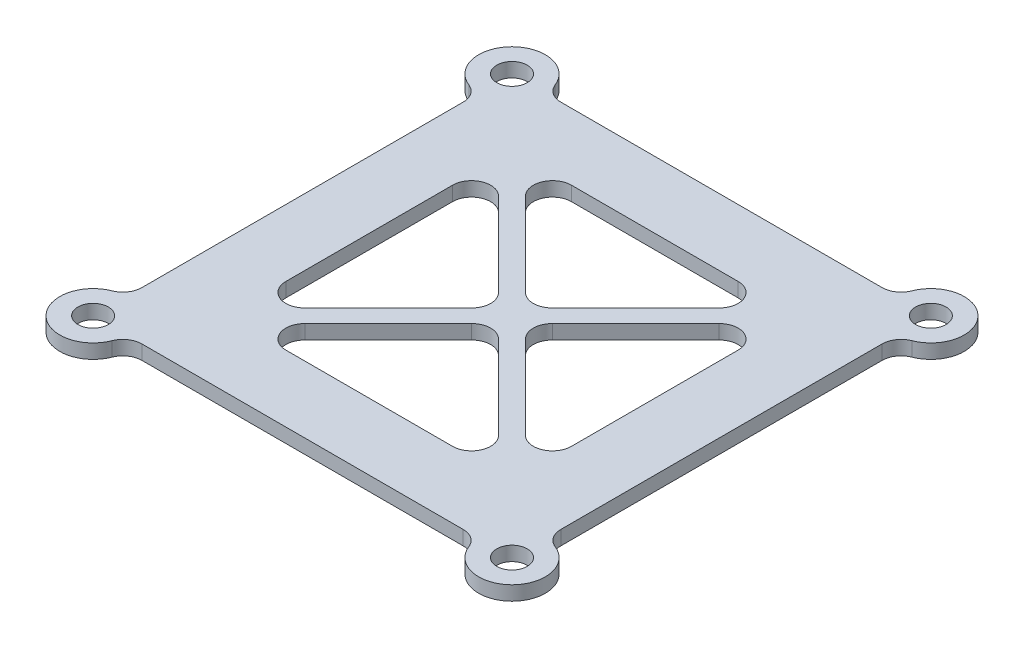
SolidWorks part; units mm, degrees
material "Thornel Mat VMA"
ref_plane "Front Plane" through (0, 0, 0) normal (0, 0, 1) x (1, 0, 0)
ref_plane "Top Plane" through (0, 0, 0) normal (0, 1, 0) x (1, 0, 0)
ref_plane "Right Plane" through (0, 0, 0) normal (1, 0, 0) x (0, 0, -1)
sketch "Sketch1" plane through (0, 0, 0) normal (0, 1, 0) x (1, 0, 0)
  line L1 (-18.5, -22) -> (18.5, -22)
  line L2 (-22, -18.5) -> (-22, 18.5)
  line L3 (-18.5, 22) -> (18.5, 22)
  line L4 (22, -18.5) -> (22, 18.5)
  line L5 (-22, -22) -> (22, 22) construction
  line L6 (-22, 22) -> (22, -22) construction
  arc A0 (-18.5, 22) -> (-22, 18.5) centre (-22, 22) ccw
  arc A1 (-22, -18.5) -> (-18.5, -22) centre (-22, -22) ccw
  arc A2 (18.5, -22) -> (22, -18.5) centre (22, -22) ccw
  arc A3 (22, 18.5) -> (18.5, 22) centre (22, 22) ccw
  point P0 (0, 0)
  dimension "D2" = 7
  dimension "D1" = 44
extrude "Boss-Extrude1" add sketch "Sketch1" along normal mid plane 1.5
fillet "Fillet1" radius 2 8 edges at (22, 0, 18.5) (18.5, 0, 22) (22, 0, -18.5) (18.5, 0, -22) (-18.5, 0, -22) (-22, 0, -18.5) (-22, 0, 18.5) (-18.5, 0, 22)
hole_wizard "Ø3.2 (3.2) Diameter Hole1" positions "Sketch3" profile "Sketch2" hole size "Ø3.2" standard "ANSI Metric"
sketch "Sketch3" plane through (0, 0.75, 0) normal (0, 1, 0) x (1, 0, 0)
  point P0 (-22, 22)
  point P3 (-22, -22)
  point P6 (22, -22)
  point P9 (22, 22)
sketch "Sketch2" plane through (-22, 0.75, -22) normal (1, 0, 0) x (0, 0, 1)
  line L0 (0, 0) -> (0, 10.9614)
  line L1 (0, 10.9614) -> (1.6, 10)
  line L2 (1.6, 10) -> (1.6, 0)
  line L5 (1.6, 0) -> (0, 0)
  line L10 (0, 10.9614) -> (-1.6, 10) construction
  line L11 (0, -6.35) -> (0, 107.95) construction
  dimension "Hole Dia." = 3.2
  dimension "Hole Depth" = 10
  dimension "Drill Angle" = 118
sketch "Sketch4" plane through (0, 0.75, 0) normal (0, 1, 0) x (1, 0, 0)
  line L2 (-15, 16.8765) -> (-15, -16.8765)
  line L3 (-15, 15) -> (-15, -15)
  line L5 (16.8765, 15) -> (-16.8765, 15)
  line L6 (15, 15) -> (-15, 15)
  line L8 (15, -16.8765) -> (15, 16.8765)
  line L9 (15, -15) -> (15, 15)
  line L10 (-15, 15) -> (15, -15)
  line L11 (-16.8765, -15) -> (16.8765, -15)
  line L12 (-15, -15) -> (15, -15)
  line L13 (15, 15) -> (-15, -15)
  line L14 (-14.2929, 15.7071) -> (15.7071, -14.2929)
  line L15 (-15.7071, 14.2929) -> (14.2929, -15.7071)
  line L16 (14.2929, 15.7071) -> (-15.7071, -14.2929)
  line L17 (15.7071, 14.2929) -> (-14.2929, -15.7071)
  dimension "D1" = 7
  dimension "D2" = 7
  dimension "D3" = 7
  dimension "D4" = 7
  dimension "D5" = 1
  dimension "D6" = 1
  dimension "D7" = 1
  dimension "D8" = 1
extrude "Cut-Extrude1" cut sketch "Sketch4" against normal blind 1.5 contours L16 L15 L3 | L16 L6 L14 | L9 L17 L14 | L15 L17 L12
fillet "Fillet2" radius 2 12 edges at (15, 0, 13.5858) (13.5858, 0, 15) (1.4142, 0, 0) (15, 0, -13.5858) (13.5858, 0, -15) (-13.5858, 0, -15) (0, 0, -1.4142) (-1.4142, 0, 0) (0, 0, 1.4142) (-13.5858, 0, 15) (-15, 0, 13.5858) (-15, 0, -13.5858)
